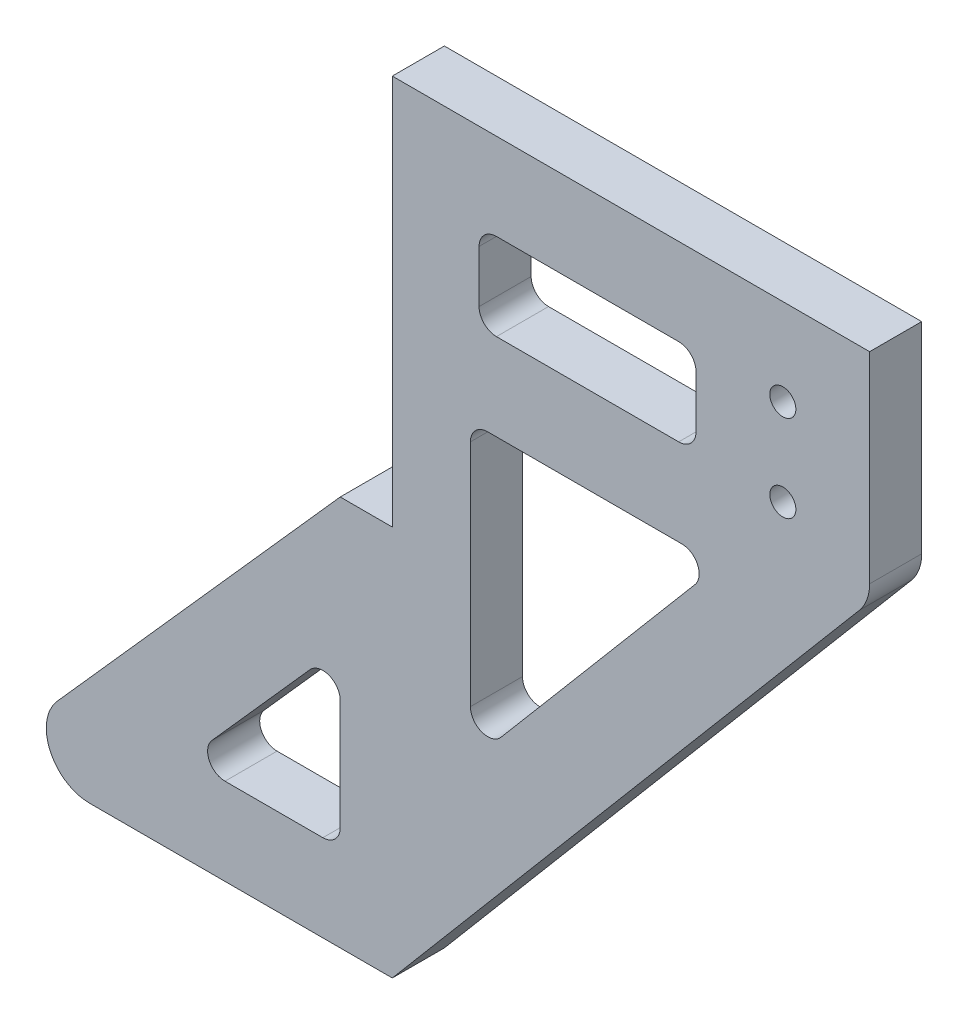
SolidWorks part; units mm, degrees
ref_plane "Front Plane" through (0, 0, 0) normal (0, 0, 1) x (1, 0, 0)
ref_plane "Top Plane" through (0, 0, 0) normal (0, 1, 0) x (1, 0, 0)
ref_plane "Right Plane" through (0, 0, 0) normal (1, 0, 0) x (0, 0, -1)
sketch "Sketch1" plane through (0, 0, 0) normal (0, 0, 1) x (1, 0, 0)
  line L1 (0, 0) -> (55, 0)
  line L4 (0, 0) -> (0, -45)
  line L5 (0, -45) -> (-6, -45)
  line L6 (-6, -45) -> (-46, -90)
  line L9 (-46, -90) -> (0, -90)
  line L11 (55, 0) -> (55, -25)
  line L15 (0, -90) -> (55, -25)
  dimension "D1" = 45
  dimension "D2" = 55
  dimension "D3" = 6
  dimension "D4" = 90
  dimension "D6" = 46
  dimension "D7" = 25
extrude "Boss-Extrude1" add sketch "Sketch1" along normal blind 6
sketch "Sketch4" plane through (0, 0, 6) normal (0, 0, 1) x (1, 0, 0)
  line L1 (9, -30) -> (9, -63.8824)
  line L3 (37.6697, -30) -> (9, -63.8824)
  line L4 (0, -90) -> (55, -25) construction
  line L6 (0, 0) -> (0, -45) construction
  line L8 (-6, -60.052) -> (-23.7316, -80)
  line L9 (-23.7316, -80) -> (-6, -80)
  line L10 (-6, -80) -> (-6, -60.052)
  line L11 (-6, -45) -> (-46, -90) construction
  line L13 (-46, -90) -> (0, -90) construction
  line L14 (10, -20) -> (35, -20)
  line L15 (55, 0) -> (0, 0) construction
  line L16 (9, -30) -> (37.6697, -30)
  line L17 (0, 0) -> (55, 0) construction
  line L18 (55, 0) -> (55, -25) construction
  line L19 (10, -20) -> (10, -10)
  line L20 (10, -10) -> (35, -10)
  line L21 (35, -20) -> (35, -10)
  circle A0 centre (45, -20) radius 1.5
  circle A1 centre (45, -10) radius 1.5
  dimension "D8" = 3
  dimension "D1" = 9
  dimension "D2" = 10
  dimension "D3" = 10
  dimension "D4" = 30
  dimension "D5" = 10
  dimension "D6" = 6
  dimension "D7" = 10
  dimension "D9" = 10
  dimension "D10" = 20
  dimension "D11" = 10
  dimension "D12" = 10
  dimension "D13" = 10
  dimension "D14" = 20
extrude "Cut-Extrude2" cut sketch "Sketch4" against normal through all both and the other way through all
fillet "Fillet1" radius 2 7 edges at (-23.7316, -80, 3) (-6, -80, 3) (-6, -60.052, 3) (10, -20, 3) (35, -20, 3) (10, -10, 3) (35, -10, 3)
fillet "Fillet2" radius 2 3 edges at (9, -63.8824, 3) (9, -30, 3) (37.6697, -30, 3)
fillet "Fillet3" radius 5 2 edges at (55, -25, 3) (-46, -90, 3)
